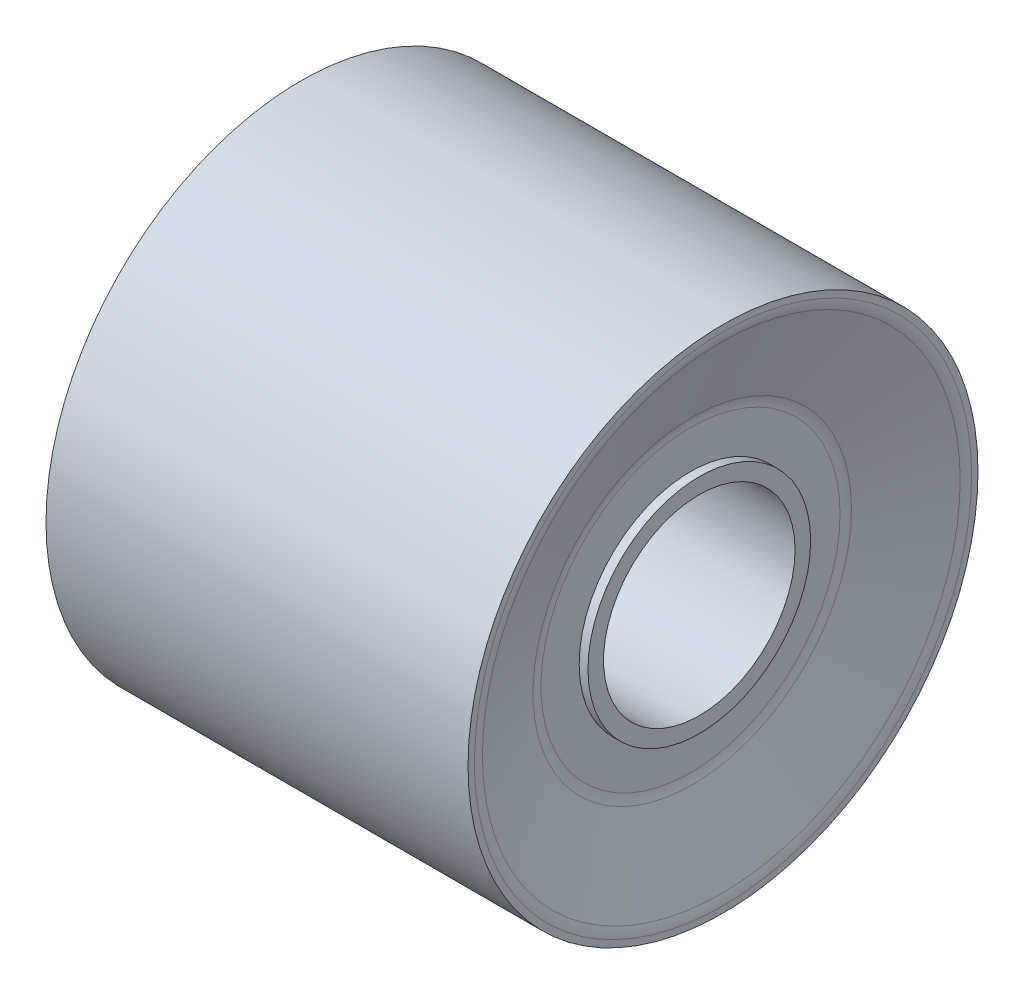
SolidWorks part; units mm, degrees
ref_plane "Front Plane" through (0, 0, 0) normal (0, 0, 1) x (1, 0, 0)
ref_plane "Top Plane" through (0, 0, 0) normal (0, 1, 0) x (1, 0, 0)
ref_plane "Right Plane" through (0, 0, 0) normal (1, 0, 0) x (0, 0, -1)
sketch "Sketch1" plane through (0, 0, 0) normal (0, 0, 1) x (1, 0, 0)
  line L0 (76.3516, 0) -> (-75.0179, 0) construction
  line L1 (-14.4122, 18.0213) -> (-14.4122, 17.2138)
  line L5 (15.4167, 17.2138) -> (15.4167, 18.0213)
  line L6 (15.4167, 18.0213) -> (-14.4122, 18.0213)
  line L8 (-11.9872, 6.7667) -> (13.1201, 6.7667)
  line L10 (-14.4122, 17.2138) -> (-11.9872, 10.9206)
  line L12 (15.4167, 17.2138) -> (13.1201, 10.9206)
  line L14 (-11.9872, 10.9206) -> (-11.9872, 7.8701)
  line L15 (-11.9872, 7.8701) -> (-12.4533, 7.8701)
  line L16 (-12.4533, 7.8701) -> (-12.4533, 6.7667)
  line L17 (-12.4533, 6.7667) -> (-11.9872, 6.7667)
  line L18 (13.1201, 10.9206) -> (13.1201, 7.8701)
  line L19 (13.1201, 7.8701) -> (13.7402, 7.8701)
  line L20 (13.7402, 7.8701) -> (13.7402, 6.7667)
  line L21 (13.7402, 6.7667) -> (13.1201, 6.7667)
revolve "Revolve1" add sketch "Sketch1" angle 360 about L0
fillet "Fillet2" radius 2 4 edges at (15.4167, 0, -17.2138) (13.1201, 0, -10.9206) (-14.4122, 0, -17.2138) (-11.9872, 0, -10.9206)
